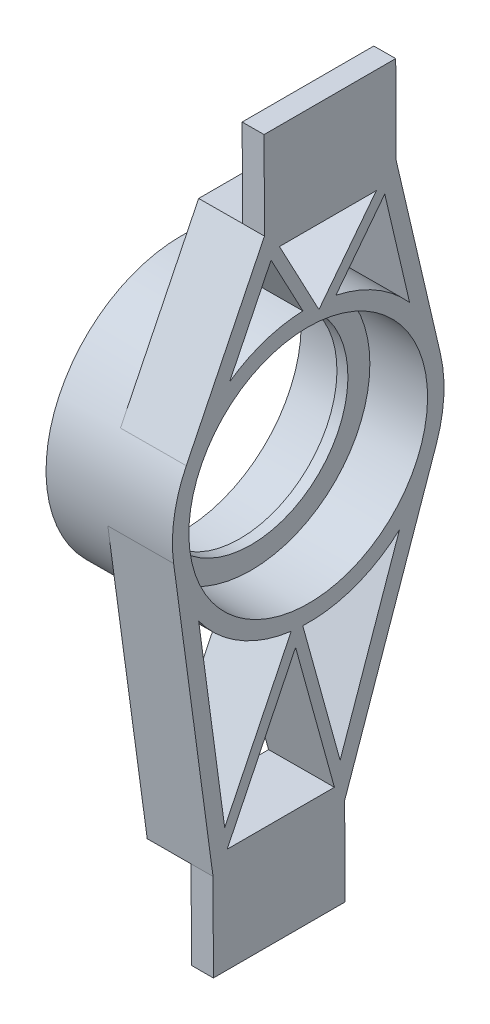
SolidWorks part; units mm, degrees
ref_plane "Front" through (0, 0, 0) normal (0, 0, 1) x (1, 0, 0)
ref_plane "Top" through (0, 0, 0) normal (0, 1, 0) x (1, 0, 0)
ref_plane "Right" through (0, 0, 0) normal (1, 0, 0) x (0, 0, -1)
sketch "Sketch1" plane through (648.2976, 2.8287, 0) normal (1, 0.0044, 0) x (0, 0, -1)
  line L0 (6.6657, 314.8388) -> (-8.8876, 137.0388) construction
  line L1 (6.6657, 314.8388) -> (-8.8876, 137.0388) construction
  line L2 (25.7157, 314.8388) -> (-12.3843, 314.8388) construction
  line L3 (10.1624, 137.0388) -> (-27.9376, 137.0388) construction
  line L4 (10.1624, 149.7388) -> (10.1624, 124.3388)
  line L5 (10.1624, 124.3388) -> (-27.9376, 124.3388)
  line L6 (-27.9376, 149.7388) -> (-27.9376, 124.3388)
  line L7 (25.7157, 302.1388) -> (25.7157, 327.5388)
  line L8 (25.7157, 327.5388) -> (-12.3843, 327.5388)
  line L9 (-12.3843, 302.1388) -> (-12.3843, 327.5388)
  line L10 (25.7157, 302.1388) -> (-12.3843, 302.1388) construction
  line L11 (10.1624, 149.7388) -> (-27.9376, 149.7388) construction
  line L12 (25.7157, 302.1388) -> (38.3045, 247.4573)
  line L13 (37.0435, 225.4943) -> (10.1624, 149.7388)
  line L14 (-27.9376, 149.7388) -> (-38.97, 233.5064)
  line L15 (-35.2143, 256.1017) -> (-12.3843, 302.1388)
  line L16 (25.7157, 302.1388) -> (3.0103, 273.0514) construction
  line L17 (3.0103, 273.0514) -> (-12.3843, 302.1388) construction
  line L18 (22.4004, 295.3116) -> (29.4559, 264.6648)
  line L19 (22.4004, 295.3116) -> (8.1736, 277.0861)
  line L20 (-1.3634, 277.9216) -> (-10.5087, 295.2013)
  line L21 (-10.5087, 295.2013) -> (-22.6157, 270.7874)
  line L22 (19.9842, 297.3763) -> (3.2669, 275.9601)
  line L23 (3.2669, 275.9601) -> (-8.0676, 297.3763)
  line L24 (-8.0676, 297.3763) -> (19.9842, 297.3763)
  line L25 (-3.4253, 199.4818) -> (10.1624, 149.7388) construction
  line L26 (-3.4253, 199.4818) -> (-27.9376, 149.7388) construction
  line L27 (26.2837, 209.4126) -> (8.8942, 160.4062)
  line L28 (8.8942, 160.4062) -> (-1.7494, 199.3712)
  line L29 (-5.1047, 199.6652) -> (-24.5203, 160.265)
  line L30 (-24.5203, 160.265) -> (-31.7994, 215.5348)
  line L31 (-3.8529, 195.0227) -> (7.2158, 154.5013)
  line L32 (7.2158, 154.5013) -> (-23.8209, 154.5013)
  line L33 (-23.8209, 154.5013) -> (-3.8529, 195.0227)
  circle A0 centre (0, 238.6388) radius 34.544
  circle A1 centre (0, 238.6388) radius 39.3065 construction
  arc A2 (29.4559, 264.6648) -> (8.1736, 277.0861) centre (0, 238.6388) ccw
  arc A3 (-1.3634, 277.9216) -> (-22.6157, 270.7874) centre (0, 238.6388) ccw
  arc A4 (-35.2143, 256.1017) -> (-38.97, 233.5064) centre (0, 238.6388) ccw
  arc A5 (-31.7994, 215.5348) -> (-5.1047, 199.6652) centre (0, 238.6388) ccw
  arc A6 (-1.7494, 199.3712) -> (26.2837, 209.4126) centre (0, 238.6388) ccw
  arc A7 (37.0435, 225.4943) -> (38.3045, 247.4573) centre (0, 238.6388) ccw
  point P5 (6.6657, 314.8388)
  point P8 (-8.8876, 137.0388)
  point P11 (10.1624, 137.0388)
  point P12 (0, 238.6388)
  point P15 (-27.9376, 137.0388)
  point P17 (25.7157, 314.8388)
  point P22 (-12.3843, 314.8388)
  dimension "D3" = 69.088
  dimension "D1" = 25.4
  dimension "D2" = 38.1
  dimension "D4" = 4.7625
  dimension "D5" = 1.5875
  dimension "D6" = 1.5875
  dimension "D7" = 4.7625
  dimension "D8" = 1.5875
  dimension "D9" = 1.5875
  dimension "D10" = 4.7625
  dimension "D11" = 4.7625
  dimension "D12" = 1.5875
  dimension "D13" = 1.5875
  dimension "D14" = 4.7625
  dimension "D15" = 1.5875
  dimension "D16" = 4.7625
  dimension "D17" = 4.7625
  dimension "D18" = 1.5875
extrude "Boss-Extrude1" add sketch "Sketch1" along normal blind 6.35 and the other way blind 12.7
sketch "Sketch2" plane through (635.5977, 2.7733, 0) normal (-1, -0.0044, 0) x (0, 0, 1)
  line L1 (-25.7157, 327.5388) -> (12.3843, 327.5388)
  line L2 (-25.7157, 327.5388) -> (-25.7157, 302.1388)
  line L3 (-25.7157, 302.1388) -> (12.3843, 302.1388)
  line L4 (12.3843, 327.5388) -> (12.3843, 302.1388)
  line L5 (-10.1624, 149.7388) -> (27.9376, 149.7388)
  line L6 (-10.1624, 149.7388) -> (-10.1624, 124.3388)
  line L7 (-10.1624, 124.3388) -> (27.9376, 124.3388)
  line L8 (27.9376, 149.7388) -> (27.9376, 124.3388)
extrude "Cut-Extrude1" cut sketch "Sketch2" against normal up to surface (12.7 mm away)
sketch "Sketch3" plane through (635.5977, 2.7733, 0) normal (-1, -0.0044, 0) x (0, 0, 1)
  circle A0 centre (0, 238.6388) radius 34.544
  circle A1 centre (0, 238.6388) radius 39.3065
extrude "Boss-Extrude2" add sketch "Sketch3" along normal offset from surface (17.526 mm away) 36.576 up to face at (653.6402, 233.7092, 0.6532)
ref_plane "Bearing Mid Plane" through (636.3597, 2.7767, 0) normal (-1, -0.0044, 0) x (0, 0, 1)
sketch "Sketch4" plane through (636.3597, 2.7767, 0) normal (-1, -0.0044, 0) x (0, 0, 1)
  circle A0 centre (0, 238.6388) radius 34.544
  circle A1 centre (0, 238.6388) radius 34.544
  circle A2 centre (0, 238.6388) radius 28.194
  dimension "D1" = 6.35
extrude "Boss-Extrude3" add sketch "Sketch4" along normal mid plane 3.175
move or copy body "Body-Move/Copy2" [suppressed] bodies to move or copy 104
move or copy body "Body-Move/Copy1" [suppressed] bodies to move or copy 104
equation "\"outer support width\"= 0.1875in"
equation "\"inner support width\"= 0.125in"
equation "\"D4@Sketch1\"=\"outer support width\""
equation "\"D5@Sketch1\"=\"inner support width\"/2"
equation "\"D6@Sketch1\"=\"inner support width\"/2"
equation "\"D7@Sketch1\"=\"outer support width\""
equation "\"D8@Sketch1\"=\"inner support width\"/2"
equation "\"D9@Sketch1\"=\"inner support width\"/2"
equation "\"D10@Sketch1\"=\"outer support width\""
equation "\"D11@Sketch1\"=\"outer support width\""
equation "\"D12@Sketch1\"=\"inner support width\"/2"
equation "\"D13@Sketch1\"=\"inner support width\"/2"
equation "\"D14@Sketch1\"=\"outer support width\""
equation "\"D15@Sketch1\"=\"inner support width\"/2"
equation "\"D16@Sketch1\"=\"outer support width\""
equation "\"D17@Sketch1\"=\"outer support width\""
equation "\"D18@Sketch1\"=\"inner support width\"/2"
